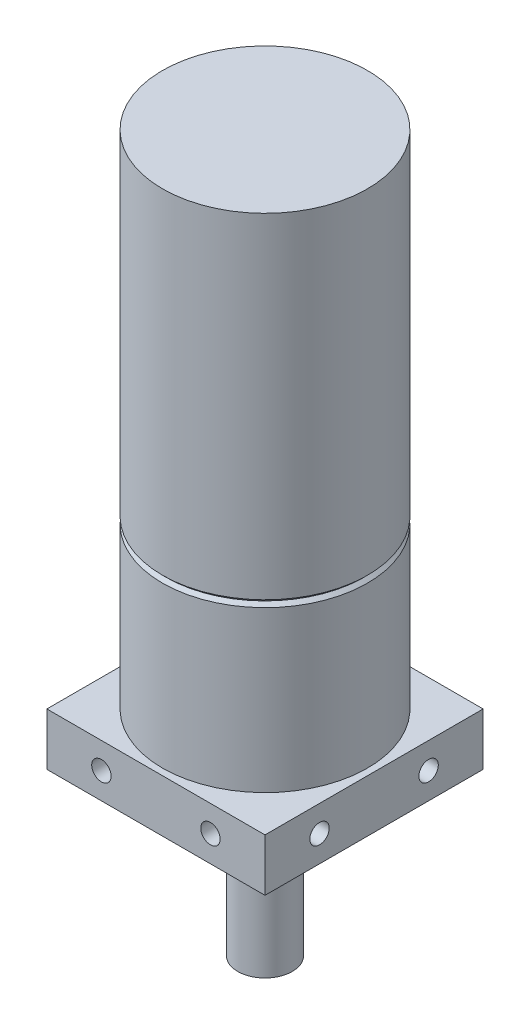
SolidWorks part; units mm, degrees
ref_plane "Front Plane" through (0, 0, 0) normal (0, 0, 1) x (1, 0, 0)
ref_plane "Top Plane" through (0, 0, 0) normal (0, 1, 0) x (1, 0, 0)
ref_plane "Right Plane" through (0, 0, 0) normal (1, 0, 0) x (0, 0, -1)
sketch "Sketch1" plane through (0, 0, 0) normal (0, 1, 0) x (1, 0, 0)
  line L0 (-12.7, -12.7) -> (12.7, 12.7) construction
  line L1 (-12.7, 12.7) -> (12.7, 12.7)
  line L2 (-12.7, 12.7) -> (-12.7, -12.7)
  line L3 (-12.7, -12.7) -> (12.7, -12.7)
  line L4 (12.7, 12.7) -> (12.7, -12.7)
  dimension "D1" = 25.4
extrude "Extrude1" add sketch "Sketch1" along normal blind 6.096
sketch "Sketch2" plane through (0, 6.096, 0) normal (0, 1, 0) x (1, 0, 0)
  circle A0 centre (0, 0) radius 11.938
  dimension "D1" = 23.876
extrude "Extrude2" add sketch "Sketch2" along normal blind 58.42
sketch "Sketch3" plane through (0, 0, 0) normal (0, -1, 0) x (1, 0, 0)
  circle A0 centre (0, 0) radius 3.175
  dimension "D1" = 6.35
extrude "Extrude3" add sketch "Sketch3" along normal blind 18.796
sketch "Sketch4" plane through (-12.7, 0, 0) normal (-1, 0, 0) x (0, 0, 1)
  line L0 (0, 6.096) -> (0, 0) construction
  line L1 (-12.7, 6.096) -> (12.7, 6.096) construction
  line L2 (-12.7, 0) -> (12.7, 0) construction
  line L3 (0, 3.048) -> (-12.7, 3.048) construction
  line L5 (12.7, 6.096) -> (12.7, 0) construction
  line L6 (0, 3.048) -> (12.7, 3.048) construction
  line L7 (-12.7, 6.096) -> (-12.7, 0) construction
  point P15 (6.35, 3.048)
  point P16 (-6.35, 3.048)
sketch "Sketch9" plane through (0, 0, 0) normal (0, -1, 0) x (1, 0, 0)
  line L0 (0, -12.7) -> (0, 12.7) construction
  line L1 (12.7, -12.7) -> (-12.7, -12.7) construction
  line L2 (-12.7, 12.7) -> (12.7, 12.7) construction
  line L3 (-12.7, 0) -> (12.7, 0) construction
  line L4 (-12.7, -12.7) -> (-12.7, 12.7) construction
  line L5 (-6.35, -12.7) -> (-6.35, 0) construction
  line L6 (-6.35, 0) -> (-6.35, 12.7) construction
  line L7 (-6.35, 12.7) -> (-6.35, 0) construction
  line L8 (12.7, -6.35) -> (-12.7, -6.35) construction
  line L9 (6.35, 0) -> (6.35, 12.7) construction
  line L10 (6.35, 0) -> (6.35, -12.7) construction
  line L11 (0, -6.35) -> (12.7, -6.35) construction
  line L12 (12.7, 12.7) -> (12.7, -12.7) construction
  line L14 (-12.7, 6.35) -> (12.6803, 6.35) construction
  point P11 (-6.35, 0)
  point P13 (0, 6.35)
  point P14 (0, -6.35)
  point P15 (6.35, 0)
  point P21 (-6.35, 6.35)
  point P31 (-6.35, -6.35)
  point P34 (6.35, -6.35)
  point P35 (6.35, 6.35)
  dimension "D1" = 6.35
  dimension "D2" = 6.35
  dimension "D3" = 6.35
  dimension "D4" = 6.35
hole_wizard "#4-40 Tapped Hole3" positions "3DSketch3" profile "Sketch11" tap size "#4-40" standard "Ansi Inch"
sketch3d "3DSketch3"
  point P0 (6.35, 0, -6.35)
  point P3 (6.35, 0, 6.35)
  point P6 (-6.35, 0, 6.35)
  point P9 (-6.35, 0, -6.35)
sketch "Sketch11" plane through (6.35, 0, -6.35) normal (1, 0, 0) x (0, 0, -1)
  line L0 (0, 0) -> (0, 3.7272)
  line L1 (0, 3.7272) -> (1.1303, 3.048)
  line L2 (1.1303, 3.048) -> (1.1303, 0)
  line L5 (1.1303, 0) -> (0, 0)
  line L10 (0, 3.7272) -> (-1.1303, 3.048) construction
  line L11 (0, -6.35) -> (0, 107.95) construction
  dimension "Tap Drill Dia." = 2.2606
  dimension "Tap Drill Depth" = 3.048
  dimension "Drill Angle" = 118
cosmetic thread "Hole Thread13" parameters "D1"=5.588, "D2"=2.8448
cosmetic thread "Hole Thread14" parameters "D1"=5.588, "D2"=2.8448
cosmetic thread "Hole Thread15" parameters "D1"=5.588, "D2"=2.8448
cosmetic thread "Hole Thread16" parameters "D1"=5.588, "D2"=2.8448
hole_wizard "#4-40 Tapped Hole4" positions "3DSketch4" profile "Sketch12" tap size "#4-40" standard "Ansi Inch"
sketch3d "3DSketch4"
  point P0 (-12.7, 3.048, -6.35)
  point P3 (-12.7, 3.048, 6.35)
sketch "Sketch12" plane through (-12.7, 3.048, -6.35) normal (0, 1, 0) x (0, 0, 1)
  line L0 (0, 0) -> (0, 4.8702)
  line L1 (0, 4.8702) -> (1.1303, 4.191)
  line L2 (1.1303, 4.191) -> (1.1303, 0)
  line L5 (1.1303, 0) -> (0, 0)
  line L10 (0, 4.8702) -> (-1.1303, 4.191) construction
  line L11 (0, -6.35) -> (0, 107.95) construction
  dimension "Tap Drill Dia." = 2.2606
  dimension "Tap Drill Depth" = 4.191
  dimension "Drill Angle" = 118
cosmetic thread "Hole Thread17" parameters "D1"=5.588, "D2"=2.8448
cosmetic thread "Hole Thread18" parameters "D1"=5.588, "D2"=2.8448
pattern_circular "CirPattern1" count 4 over 360 about axis through (0, -18.796, 0) along (0, 1, 0) of "#4-40 Tapped Hole4"
sketch "Sketch13" plane through (0, 0, 0) normal (0, 0, 1) x (1, 0, 0)
  line L0 (0, 64.516) -> (0, 0) construction
  line L1 (11.938, 64.516) -> (-11.938, 64.516) construction
  line L2 (-11.938, 25.146) -> (0, 25.146) construction
  line L3 (-11.938, 64.516) -> (-11.938, 6.096) construction
  line L4 (-12.7, 6.096) -> (12.7, 6.096) construction
  line L5 (-11.938, 25.5429) -> (-11.5411, 25.146)
  line L6 (-11.5411, 25.146) -> (-11.938, 24.7491)
  line L7 (-11.938, 24.7491) -> (-11.938, 25.5429)
  dimension "D1" = 19.05
  dimension "D2" = 0.7937
revolve "Cut-Revolve1" cut sketch "Sketch13" angle 360 about L0
